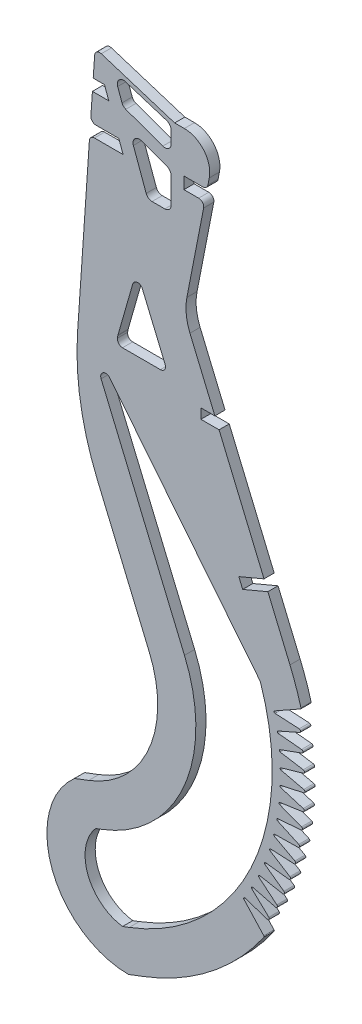
SolidWorks part; units mm, degrees
ref_plane "Front Plane" through (0, 0, 0) normal (0, 0, 1) x (1, 0, 0)
ref_plane "Top Plane" through (0, 0, 0) normal (0, 1, 0) x (1, 0, 0)
ref_plane "Right Plane" through (0, 0, 0) normal (1, 0, 0) x (0, 0, -1)
sketch "Sketch1" plane through (0, 0, 0) normal (0, 0, 1) x (1, 0, 0)
  line L0 (-16.5187, -7.7319) -> (114.701, -368.2552) construction
  line L1 (18, -15.3797) -> (18, -394.6359) construction
  line L2 (280.4309, 1) -> (280.4309, -315) construction
  line L3 (280.4309, 1) -> (-91.1971, 1) construction
  line L4 (-8.0392, -14.8021) -> (-6.3291, -19.5006)
  line L5 (-4.8648, -20.9649) -> (9.6621, -26.2522)
  line L6 (12.95, -19.1014) -> (12.95, -23.95)
  line L7 (-16.5187, -7.7319) -> (-1.2734, -49.6181) construction
  line L8 (18, -48.25) -> (18, -15.3797) construction
  line L9 (-8.0862, -14.8192) -> (-6.3761, -19.5177) construction
  line L10 (-4.8819, -21.0119) -> (9.6449, -26.2992) construction
  line L11 (-4.9828, -11.5807) -> (11.2541, -16.7178) construction
  line L12 (-4.9979, -11.6283) -> (11.239, -16.7655)
  line L13 (-1.8643, -31.7674) -> (3.1659, -45.5879)
  line L14 (13, -19.1014) -> (13, -23.95) construction
  line L15 (-1.9113, -31.7845) -> (3.1189, -45.6051) construction
  line L16 (5.4682, -47.25) -> (10.5, -47.25) construction
  line L17 (13, -34.5918) -> (13, -44.75) construction
  line L18 (11.3551, -32.2425) -> (1.293, -28.5802) construction
  line L19 (280.4309, -315) -> (-159.7316, -315) construction
  line L20 (70.3658, -16) -> (14.3672, -16) construction
  line L21 (15.7695, -9) -> (138.1, -9) construction
  line L22 (-14.4991, -6.867) -> (14.3672, -16)
  line L23 (14.3672, -16) -> (18.1539, -16)
  line L24 (27.9685, -27.9164) -> (27.4395, -30.6258)
  line L25 (18, -78.9705) -> (49.0911, -315) construction
  line L26 (49.0911, -315) -> (-38.1516, -315) construction
  line L27 (-38.1516, -315) -> (-17.0977, -8.6367) construction
  line L28 (9.6449, -26.2992) -> (-4.8819, -21.0119) construction
  line L29 (-6.3761, -19.5177) -> (-11.322, -5.929) construction
  line L30 (5.4682, -47.2) -> (10.5, -47.2)
  line L31 (12.95, -34.5918) -> (12.95, -44.75)
  line L32 (11.3379, -32.2895) -> (1.2759, -28.6272)
  line L33 (20.3682, -84.5884) -> (30.1739, -107.85)
  line L34 (1.7859, -312.8881) -> (-3.7971, -315)
  line L35 (24.6282, -111.8) -> (-35.8718, -111.8) construction
  line L36 (24.6282, -107.8) -> (35.12, -107.8) construction
  line L37 (170.6751, -107.8) -> (24.6282, -107.8) construction
  line L38 (-16.0261, -152.7163) -> (4.3996, -201.1711)
  line L39 (-19.4424, -256.769) -> (-25.0254, -258.8808)
  line L40 (-23.7958, -106.1022) -> (-19.1675, -38.7554)
  line L41 (-44.393, -85.4233) -> (4.3996, -201.1711) construction
  line L42 (27.9685, -27.9164) -> (18, -78.9705) construction
  line L43 (18, -78.9705) -> (59.6881, -177.8646) construction
  line L44 (1.6573, -78.8176) -> (10.5963, -100.0231)
  line L45 (-3.5212, -298.8583) -> (-6.1198, -299.8413)
  line L46 (-14.1354, -270.7987) -> (-16.7339, -271.7817)
  line L47 (-14.5606, -117.5769) -> (18.2218, -195.3444)
  line L48 (-6.1418, -102.8) -> (8.7534, -102.8)
  line L49 (47.7748, -188.9944) -> (-11.1577, -115.5483)
  line L50 (24.6282, -107.8) -> (-35.8718, -107.8) construction
  line L51 (-2.204, -146.8897) -> (18.2218, -195.3444) construction
  line L52 (-2.1084, -79.0438) -> (-7.9327, -99.3791)
  line L53 (6.5461, -90.415) -> (45.866, -183.6912) construction
  line L54 (-8.831, -107.1306) -> (-3.2662, -26.1539) construction
  line L55 (-3.2662, -26.1539) -> (12.0508, -31) construction
  line L56 (12.0508, -31) -> (12.0832, -31) construction
  line L57 (12.0832, -31) -> (4.4463, -70.1123) construction
  line L58 (24.6282, -107.8) -> (24.6282, -111.8) construction
  line L59 (64.1037, -190.6477) -> (52.4488, -197.2188)
  line L60 (52.4488, -197.2188) -> (65.8087, -197.9459)
  line L61 (65.8087, -197.9459) -> (53.5675, -203.3465)
  line L62 (53.5675, -203.3465) -> (66.8849, -204.6344)
  line L63 (66.8849, -204.6344) -> (54.3122, -209.2105)
  line L64 (54.3122, -209.2105) -> (67.5148, -211.3797)
  line L65 (67.5148, -211.3797) -> (54.6661, -215.1111)
  line L66 (54.6661, -215.1111) -> (67.6956, -218.1519)
  line L67 (67.6956, -218.1519) -> (54.6275, -221.0221)
  line L68 (54.6275, -221.0221) -> (67.4264, -224.9211)
  line L69 (67.4264, -224.9211) -> (54.1965, -226.9176)
  line L70 (54.1965, -226.9176) -> (66.7084, -231.6575)
  line L71 (66.7084, -231.6575) -> (53.3752, -232.7714)
  line L72 (53.3752, -232.7714) -> (65.5449, -238.3314)
  line L73 (65.5449, -238.3314) -> (52.1672, -238.5578)
  line L74 (52.1672, -238.5578) -> (63.9409, -244.9134)
  line L75 (63.9409, -244.9134) -> (50.5777, -244.2512)
  line L76 (50.5777, -244.2512) -> (61.9035, -251.3744)
  line L77 (61.9035, -251.3744) -> (48.6137, -249.8266)
  line L78 (48.6137, -249.8266) -> (59.4417, -257.6859)
  line L79 (59.4417, -257.6859) -> (46.284, -255.2593)
  line L80 (46.284, -255.2593) -> (56.5664, -263.82)
  line L81 (56.5664, -263.82) -> (43.5988, -260.5254)
  line L82 (43.5988, -260.5254) -> (53.2903, -269.7497)
  line L83 (53.2903, -269.7497) -> (40.57, -265.6016)
  line L84 (40.57, -265.6016) -> (49.6278, -275.4489)
  line L85 (-40.2112, -64.0061) -> (-44.393, -85.4233) construction
  line L86 (-40.2112, -64.0061) -> (-40.2112, -64.0061) construction
  line L87 (-40.2112, -64.0061) -> (-40.2112, -64.0061) construction
  line L88 (24.6282, -111.8) -> (35.12, -111.8) construction
  line L89 (24.6282, -111.8) -> (170.6751, -111.8) construction
  line L90 (24.6782, -111.75) -> (31.818, -111.75)
  line L91 (24.6782, -107.85) -> (24.6782, -111.75)
  line L92 (24.6782, -107.85) -> (30.1739, -107.85)
  line L93 (31.818, -111.75) -> (49.4946, -153.6833)
  line L94 (24.6782, -107.85) -> (35.12, -107.85) construction
  line L95 (24.6782, -111.75) -> (35.12, -111.75) construction
  line L96 (-7.5976, -32.2425) -> (-5.9051, -36.8925)
  line L97 (20.3682, -84.5884) -> (59.6881, -177.8646) construction
  line L98 (-5.9051, -36.8925) -> (-17.1723, -36.8925)
  line L99 (-7.5976, -32.2425) -> (-16.5778, -32.2425)
  line L100 (25.4766, -32.2425) -> (18, -32.2425)
  line L101 (18, -32.2425) -> (18, -36.8925)
  line L102 (18, -36.8925) -> (23.7876, -36.8925)
  line L103 (25.7506, -39.2758) -> (19.1683, -72.9869)
  line L104 (-18.5731, -30.1054) -> (-17.9759, -21.4155)
  line L105 (27.9685, -27.9164) -> (19.1683, -72.9869) construction
  line L106 (-13.2308, -16.7655) -> (-11.5383, -21.4155)
  line L107 (-23.7958, -106.1022) -> (-17.0977, -8.6367) construction
  line L108 (-13.2308, -16.7655) -> (-17.6564, -16.7655)
  line L109 (-11.5383, -21.4155) -> (-17.9759, -21.4155)
  line L110 (-17.6564, -16.7655) -> (-17.0977, -8.6367)
  line L111 (49.4752, -153.6372) -> (39.5675, -157.8138) construction
  line L112 (39.5869, -157.8598) -> (41.1018, -161.4536)
  line L113 (41.1213, -161.4997) -> (51.029, -157.3231) construction
  line L114 (49.4946, -153.6833) -> (39.5869, -157.8598)
  line L115 (41.1018, -161.4536) -> (51.0095, -157.2771)
  line L116 (51.0095, -157.2771) -> (59.6881, -177.8646)
  arc A0 (-4.8819, -21.0119) -> (-6.3761, -19.5177) centre (-4.0268, -18.6627) cw construction
  arc A1 (9.6449, -26.2992) -> (13, -23.95) centre (10.5, -23.95) ccw construction
  arc A2 (11.2541, -16.7178) -> (13, -19.1014) centre (10.5, -19.1014) cw construction
  arc A3 (-8.0862, -14.8192) -> (-4.9828, -11.5807) centre (-5.7369, -13.9642) cw construction
  arc A4 (11.3551, -32.2425) -> (13, -34.5918) centre (10.5, -34.5918) cw construction
  arc A5 (13, -44.75) -> (10.5, -47.25) centre (10.5, -44.75) cw construction
  arc A6 (5.4682, -47.25) -> (3.1189, -45.6051) centre (5.4682, -44.75) cw construction
  arc A7 (-1.9113, -31.7845) -> (1.293, -28.5802) centre (0.4379, -30.9295) cw construction
  arc A8 (18.1539, -16) -> (27.9685, -27.9164) centre (18.1539, -26) cw
  arc A9 (-4.8648, -20.9649) -> (-6.3291, -19.5006) centre (-4.0268, -18.6627) cw
  arc A10 (9.6621, -26.2522) -> (12.95, -23.95) centre (10.5, -23.95) ccw
  arc A11 (11.239, -16.7655) -> (12.95, -19.1014) centre (10.5, -19.1014) cw
  arc A12 (-8.0392, -14.8021) -> (-4.9979, -11.6283) centre (-5.7369, -13.9642) cw
  arc A13 (5.4682, -47.2) -> (3.1659, -45.5879) centre (5.4682, -44.75) cw
  arc A14 (12.95, -44.75) -> (10.5, -47.2) centre (10.5, -44.75) cw
  arc A15 (11.3379, -32.2895) -> (12.95, -34.5918) centre (10.5, -34.5918) cw
  arc A16 (-1.8643, -31.7674) -> (1.2759, -28.6272) centre (0.4379, -30.9295) cw
  arc A17 (-14.4991, -6.867) -> (-17.0977, -8.6367) centre (-15.1024, -8.7738) ccw
  arc A18 (59.6881, -177.8646) -> (64.1037, -190.6477) centre (-34.3023, -217.4855) cw
  arc A19 (-17.1723, -36.8925) -> (-19.1675, -38.7554) centre (-17.1723, -38.8925) ccw
  arc A20 (-16.5778, -32.2425) -> (-18.5731, -30.1054) centre (-16.5778, -30.2425) cw
  arc A21 (4.3996, -201.1711) -> (-19.4424, -256.769) centre (-34.3023, -217.4855) cw
  arc A22 (-25.0254, -258.8808) -> (-3.7971, -315) centre (-3.7971, -282.9254) ccw
  arc A23 (-16.0261, -152.7163) -> (-23.7958, -106.1022) centre (77.9642, -113.0954) cw
  arc A24 (19.1683, -72.9869) -> (20.3682, -84.5884) centre (38.7977, -76.8196) ccw
  arc A25 (48.1094, -189.6051) -> (-3.5212, -298.8583) centre (-34.3023, -217.4855) cw
  arc A26 (-16.7339, -271.7817) -> (-6.1198, -299.8413) centre (-3.7971, -282.9254) ccw
  arc A27 (18.2218, -195.3444) -> (-14.1354, -270.7987) centre (-34.3023, -217.4855) cw
  arc A28 (-8.1208, -100.5107) -> (-7.9858, -99.62) centre (77.9642, -113.0954) cw
  arc A29 (-3.2662, -26.1539) -> (-3.2662, -26.1539) centre (-3.2662, -26.1539) ccw
  arc A30 (12.0832, -31) -> (12.0832, -31) centre (12.0832, -31) cw
  arc A31 (-2.204, -146.8897) -> (-8.831, -107.1306) centre (77.9642, -113.0954) cw construction
  arc A32 (-6.1418, -102.8) -> (-8.1208, -100.5107) centre (-6.1418, -100.8) cw
  arc A33 (4.4463, -70.1123) -> (6.5461, -90.415) centre (38.7977, -76.8196) ccw construction
  arc A34 (-7.9858, -99.62) -> (-7.9327, -99.3791) centre (-6.01, -99.9298) cw
  arc A35 (1.6573, -78.8176) -> (-2.1084, -79.0438) centre (-0.1857, -79.5945) ccw
  arc A36 (45.866, -183.6912) -> (-3.5212, -298.8583) centre (-34.3023, -217.4855) cw construction
  arc A37 (47.7748, -188.9944) -> (48.1094, -189.6051) centre (46.2149, -190.2461) cw
  arc A38 (-11.1577, -115.5483) -> (-14.5606, -117.5769) centre (-12.7176, -116.8) ccw
  arc A39 (10.5963, -100.0231) -> (8.7534, -102.8) centre (8.7534, -100.8) cw
  arc A40 (16.3788, -196.1213) -> (-14.843, -268.9281) centre (-34.3023, -217.4855) cw construction
  arc A41 (50.0039, -188.9642) -> (-2.8136, -300.729) centre (-34.3023, -217.4855) cw construction
  arc A43 (49.6278, -275.4489) -> (1.7859, -312.8881) centre (-34.3023, -217.4855) cw
  arc A44 (59.6881, -177.8646) -> (1.7859, -312.8881) centre (-34.3023, -217.4855) cw construction
  arc A45 (-40.2112, -64.0061) -> (-40.2112, -64.0061) centre (-40.2112, -64.0061) cw construction
  arc A46 (-40.2112, -64.0061) -> (-40.2112, -64.0061) centre (-40.2112, -64.0061) cw construction
  arc A47 (23.7876, -36.8925) -> (25.7506, -39.2758) centre (23.7876, -38.8925) cw
  arc A48 (25.4766, -32.2425) -> (27.4395, -30.6258) centre (25.4766, -30.2425) ccw
  point P32 (13, -17.2702)
  point P35 (-11.322, -5.929)
  point P75 (30.2952, -16)
  point P88 (-16.9234, -6.1)
  point P108 (-25.461, -130.3344)
  point P153 (66.231, -200.2502)
  point P216 (-19.0395, -36.8925)
  point P219 (-18.72, -32.2425)
  point P222 (26.2159, -36.8925)
  dimension "D1" = 2.5
  dimension "D2" = 2.5
  dimension "D6" = 10
  dimension "D8" = 2
  dimension "D9" = 102
  dimension "D11" = 102
  dimension "D13" = 20
  dimension "D16" = 2
  dimension "D15" = 2
  dimension "D22" = 2
  dimension "D3" = 280
  dimension "D4" = 7
  dimension "D5" = 5
  dimension "D12" = 5
  dimension "D19" = 5
  dimension "D21" = 4.65
  dimension "D23" = 4.65
  dimension "D7" = 0.05
  dimension "D10" = 60
  dimension "D14" = 15
  dimension "D17" = 2
  dimension "D18" = 2
  dimension "D20" = 0.05
  dimension "D24" = 0.05
extrude "Boss-Extrude1" add sketch "Sketch1" along normal blind 4 contours A16 L13 A13 L30 A14 L31 A15 L32 | A12 L4 A9 L5 A10 L6 A11 L12 | L60 L61 L62 L63 L64 L65 L66 L67 L68 L69 L70 L71 L72 L73 L74 L75 L76 L77 L78 L79 L80 L81 L82 L83 L84 A43 L34 A22 L39 A21 L38 A23 L40 A19 L98 L96 L99 A20 L104 L109 L106 L108 L110 A17 L22 L23 A8 L24 A48 L100 L101 L102 A47 L103 A24 L33 L92 L91 L90 L93 L114 L112 L115 L116 A18 L59 | L48 A39 L44 A35 L52 A34 A28 A32 | A38 L47 A27 L46 A26 L45 A25 A37 L49
fillet "Fillet1" radius 0.4 15 edges at (64.1037, -190.6477, 2) (49.6278, -275.4489, 2) (40.57, -265.6016, 2) (43.5988, -260.5254, 2) (46.284, -255.2593, 2) (48.6137, -249.8266, 2) (50.5777, -244.2512, 2) (52.1672, -238.5578, 2) (53.3752, -232.7714, 2) (54.1965, -226.9176, 2) (54.6275, -221.0221, 2) (54.6661, -215.1111, 2) (54.3122, -209.2105, 2) (53.5675, -203.3465, 2) (52.4488, -197.2188, 2)
fillet "Fillet2" radius 0.6 12 edges at (53.2903, -269.7497, 2) (56.5664, -263.82, 2) (59.4417, -257.6859, 2) (61.9035, -251.3744, 2) (63.9409, -244.9134, 2) (65.5449, -238.3314, 2) (66.7084, -231.6575, 2) (67.4264, -224.9211, 2) (67.6956, -218.1519, 2) (67.5148, -211.3797, 2) (66.8849, -204.6344, 2) (65.8087, -197.9459, 2)
equation "\"D23@Sketch1\"=\"D21@Sketch1\""
